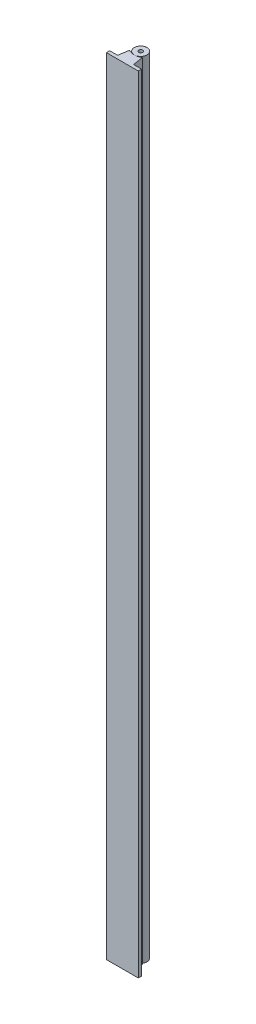
SolidWorks part; units mm, degrees
material "Acero al carbono no aleado"
ref_plane "Alzado" through (0, 0, 0) normal (0, 0, 1) x (1, 0, 0)
ref_plane "Planta" through (0, 0, 0) normal (0, 1, 0) x (1, 0, 0)
ref_plane "Vista lateral" through (0, 0, 0) normal (1, 0, 0) x (0, 0, -1)
sketch "Croquis2" plane through (0, 0, 0) normal (0, 1, 0) x (1, 0, 0)
  line L0 (-27.2764, -6.7227) -> (10.8236, -6.7227)
  line L1 (2.7236, -2.6227) -> (0.7236, 10.3773)
  line L2 (-17.2764, -2.6227) -> (-15.2764, 10.3773)
  line L3 (-27.2764, -2.6227) -> (-17.2764, -2.6227)
  line L4 (12.7236, -2.6227) -> (2.7236, -2.6227)
  line L5 (12.7236, -6.7227) -> (12.7236, -2.6227)
  line L6 (10.8236, -6.7227) -> (12.7236, -6.7227)
  line L7 (-27.2764, -6.7227) -> (-27.2764, -2.6227)
  line L8 (-7.2764, 8.2337) -> (-7.2764, 16.2337) construction
  arc A0 (-15.2764, 10.3773) -> (0.7236, 10.3773) centre (-7.2764, 24.2337) ccw
  circle A1 centre (-7.2764, 16.2337) radius 8
  dimension "D1" = 40
  dimension "D2" = 8
extrude "Saliente-Extruir1" add sketch "Croquis2" along normal blind 985
sketch "Croquis3" plane through (0, 0, 0) normal (0, -1, 0) x (1, 0, 0)
  line L0 (-7.2764, -24.2337) -> (-7.2764, -8.2337) construction
  arc A0 (0.7236, -10.3773) -> (-15.2764, -10.3773) centre (-7.2764, -24.2337) ccw construction
  circle A1 centre (-7.2764, -16.2337) radius 2.5
extrude "Cortar-Extruir1" cut sketch "Croquis3" against normal blind 15
sketch "Croquis4" plane through (0, 985, 0) normal (0, 1, 0) x (1, 0, 0)
  line L0 (-7.2764, 24.2337) -> (-7.2764, 8.2337) construction
  circle A0 centre (-7.2764, 16.2337) radius 8 construction
  arc A1 (-15.2764, 10.3773) -> (0.7236, 10.3773) centre (-7.2764, 24.2337) ccw construction
  circle A2 centre (-7.2764, 16.2337) radius 2.5
extrude "Cortar-Extruir2" cut sketch "Croquis4" against normal blind 15
